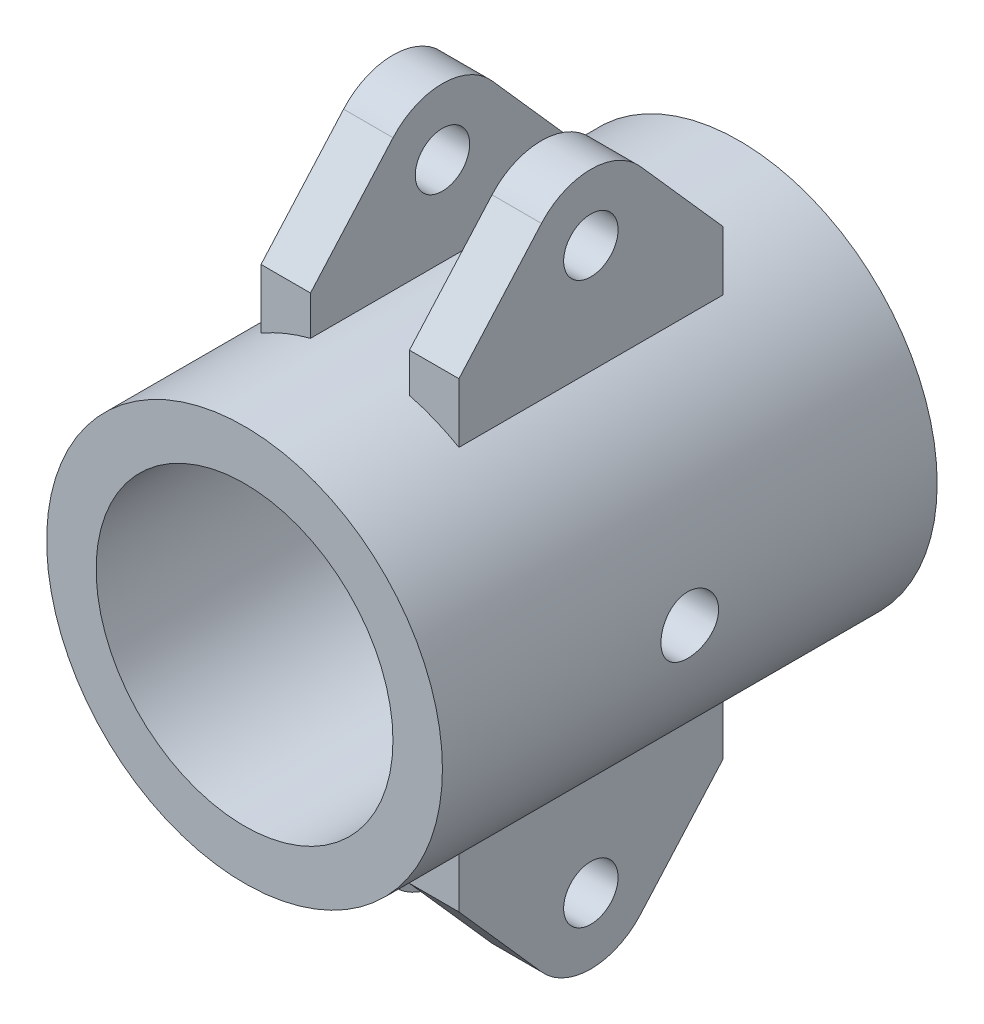
SolidWorks part; units mm, degrees
ref_plane "正面(Front)" through (0, 0, 0) normal (0, 0, 1) x (1, 0, 0)
ref_plane "平面(Top)" through (0, 0, 0) normal (0, 1, 0) x (1, 0, 0)
ref_plane "右側面(Right)" through (0, 0, 0) normal (1, 0, 0) x (0, 0, -1)
sketch "ｽｹｯﾁ1" plane through (0, 0, 0) normal (0, 0, 1) x (1, 0, 0)
  circle A0 centre (0, 0) radius 9
  circle A1 centre (0, 0) radius 12
  dimension "D1" = 18
  dimension "D2" = 24
extrude "ﾎﾞｽ - 押し出し1" add sketch "ｽｹｯﾁ1" along normal blind 30
ref_plane "平面1" through (3, 0, 0) normal (1, 0, 0) x (0, 0, -1)
sketch "ｽｹｯﾁ2" plane through (3, 0, 0) normal (1, 0, 0) x (0, 0, -1)
  line L0 (-23, 9) -> (-23, 14)
  line L1 (-23, 14) -> (-17.9945, 19.652)
  line L2 (-12.0055, 19.652) -> (-7, 14)
  line L3 (-7, 14) -> (-7, 9)
  line L4 (-7, 9) -> (-23, 9)
  line L5 (0, 0) -> (-30, 0) construction
  line L6 (-30, 12) -> (-30, -12) construction
  line L7 (-15, 0) -> (-15, 23.4871) construction
  line L8 (0, 12) -> (-30, 12) construction
  arc A0 (-17.9945, 19.652) -> (-12.0055, 19.652) centre (-15, 17) cw
  circle A2 centre (-15, 17) radius 1.65
  dimension "D2" = 4
  dimension "D3" = 3.3
  dimension "D5" = 5
  dimension "D1" = 9
  dimension "D4" = 5
  dimension "D6" = 16
extrude "ﾎﾞｽ - 押し出し2" add sketch "ｽｹｯﾁ2" along normal blind 3
mirror "ﾐﾗｰ1" about plane through (0, 0, 0) normal (1, 0, 0) of "ﾎﾞｽ - 押し出し2"
sketch "ｽｹｯﾁ3" plane through (0, 0, 0) normal (1, 0, 0) x (0, 0, -1)
  line L0 (0, 0) -> (-30, 0) construction
  line L1 (-30, 12) -> (-30, -12) construction
  circle A0 centre (-15, 0) radius 1.75
  dimension "D1" = 3.5
extrude "ｶｯﾄ - 押し出し1" cut sketch "ｽｹｯﾁ3" against normal through all both and the other way through all
mirror "ﾐﾗｰ2" about plane through (0, 0, 0) normal (0, 1, 0) of "ﾐﾗｰ1", "ﾎﾞｽ - 押し出し2"
